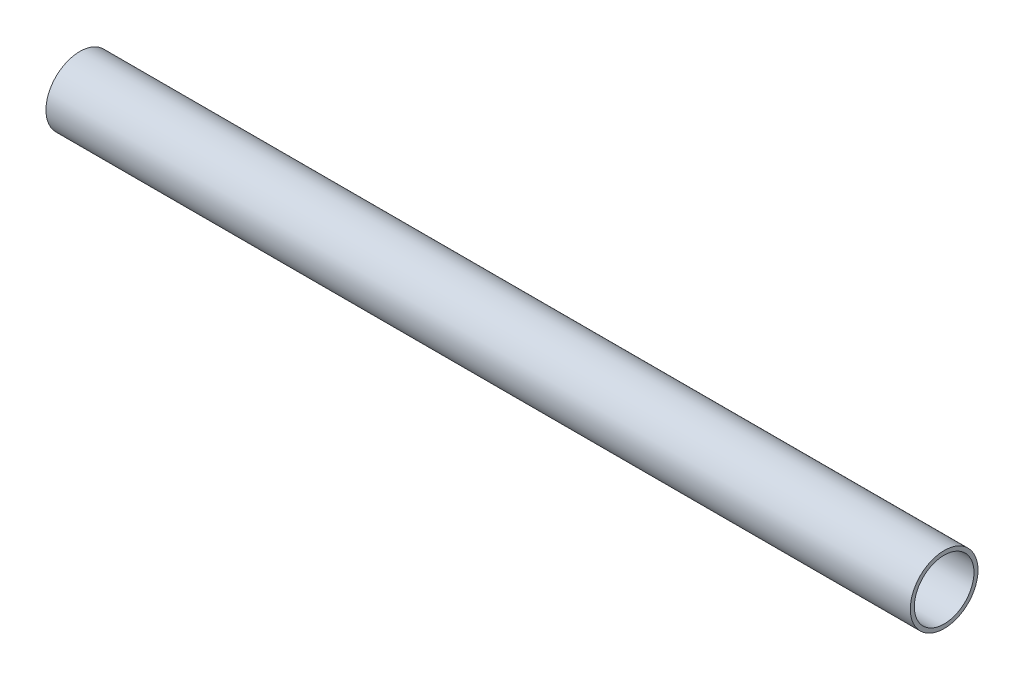
SolidWorks part; units mm, degrees
material "Corrugated Paper"
ref_plane "Front Plane" through (0, 0, 0) normal (0, 0, 1) x (1, 0, 0)
ref_plane "Top Plane" through (0, 0, 0) normal (0, 1, 0) x (1, 0, 0)
ref_plane "Right Plane" through (0, 0, 0) normal (1, 0, 0) x (0, 0, -1)
sketch "Sketch1" plane through (0, 0, 0) normal (1, 0, 0) x (0, 0, -1)
  circle A0 centre (0, 0) radius 36.9
  circle A1 centre (0, 0) radius 41.9
  dimension "D1" = 83.8
  dimension "D2" = 73.8
extrude "Boss-Extrude1" add sketch "Sketch1" along normal blind 1070
sketch "Sketch2" plane through (0, 0, 0) normal (-1, 0, 0) x (0, 0, 1)
  line L0 (0, 0) -> (0, 52.3045)
  line L1 (0, 0) -> (45.297, -26.1523)
  line L2 (0, 0) -> (-45.297, -26.1523)
  point P8 (0, 0)
  dimension "D1" = 52.3045
  dimension "D2" = 3
ref_plane "Plane1" through (610, 0, 0) normal (1, 0, 0) x (0, 0, -1)
sketch "Sketch3" plane through (610, 0, 0) normal (1, 0, 0) x (0, 0, -1)
  circle A0 centre (0, 0) radius 36.9
  dimension "D1" = 73.8
